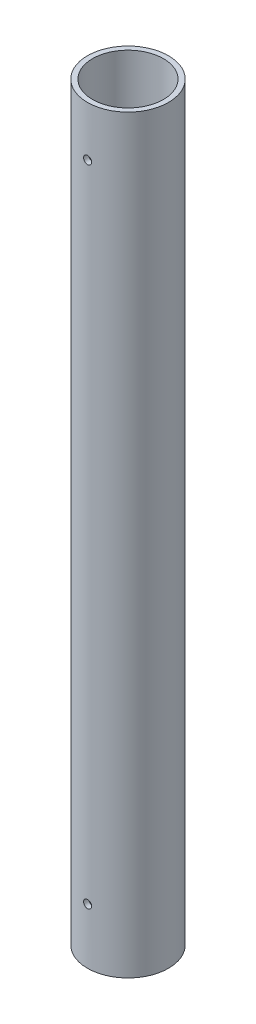
SolidWorks part; units mm, degrees
material "Default"
ref_plane "Front Plane" through (0, 0, 0) normal (0, 0, 1) x (1, 0, 0)
ref_plane "Top Plane" through (0, 0, 0) normal (0, 1, 0) x (1, 0, 0)
ref_plane "Right Plane" through (0, 0, 0) normal (1, 0, 0) x (0, 0, -1)
sketch "Sketch2" plane through (0, 0, 0) normal (0, 1, 0) x (1, 0, 0)
  circle A0 centre (0, 0) radius 8
  circle A1 centre (0, 0) radius 7
extrude "Boss-Extrude1" add sketch "Sketch2" along normal blind 148.1292 contours A0 | A1
ref_plane "Plane1" through (0, 0, 8) normal (0, 0, 1) x (1, 0, 0)
sketch "Sketch3" plane through (0, 0, 8) normal (0, 0, 1) x (1, 0, 0)
  line L0 (0, 0) -> (0, 11) construction
  line L1 (0, 148.1292) -> (0, 138.2792) construction
  line L2 (7, 148.1292) -> (-7, 148.1292) construction
  circle A0 centre (0, 11) radius 1
  circle A1 centre (0, 138.2792) radius 1
  dimension "D2" = 9.85
  dimension "D1" = 11
hole_wizard "M2 Tapped Hole1" positions "Sketch4" profile "Sketch5" tap size "M2" standard "ISO" end condition through all
sketch "Sketch4" plane through (0, 0, 8) normal (0, 0, 1) x (1, 0, 0)
  point P0 (0, 11)
  point P3 (0, 138.2792)
sketch "Sketch5" plane through (0, 11, 8) normal (1, 0, 0) x (0, -1, 0)
  line L0 (0, 0) -> (0, 16)
  line L1 (0, 16) -> (0.8, 16)
  line L2 (0.8, 16) -> (0.8, 0)
  line L5 (0.8, 0) -> (0, 0)
  line L11 (0, -6.35) -> (0, 107.95) construction
  dimension "Thru Tap Drill Dia." = 1.6
  dimension "Thru Tap Drill Depth" = 16
cosmetic thread "Hole Thread1" parameters "D2"=2
cosmetic thread "Hole Thread2" parameters "D2"=2
